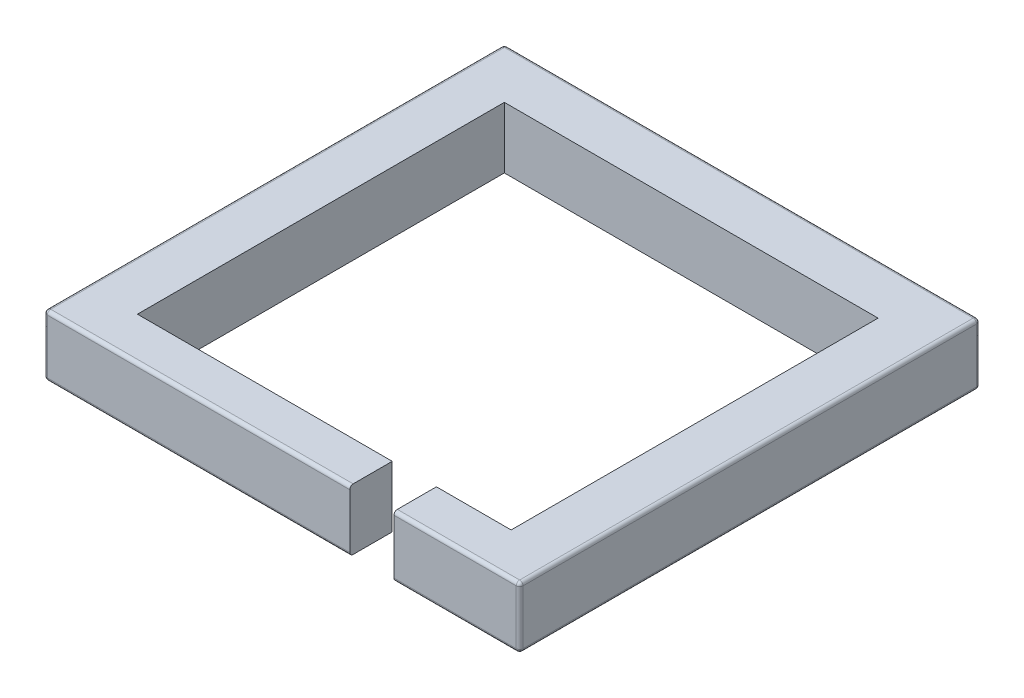
SolidWorks part; units mm, degrees
material "Polyurethane Foam Rigid"
ref_plane "Front Plane" through (0, 0, 0) normal (0, 0, 1) x (1, 0, 0)
ref_plane "Top Plane" through (0, 0, 0) normal (0, 1, 0) x (1, 0, 0)
ref_plane "Right Plane" through (0, 0, 0) normal (1, 0, 0) x (0, 0, -1)
sketch "Sketch2" plane through (0, 0, 0) normal (0, 1, 0) x (1, 0, 0)
  line L0 (-444.5, 438.15) -> (444.5, 438.15)
  line L1 (-349.25, -342.9) -> (349.25, -342.9)
  line L2 (-349.25, -342.9) -> (-349.25, 342.9)
  line L3 (-349.25, 342.9) -> (349.25, 342.9)
  line L4 (349.25, -342.9) -> (349.25, 342.9)
  line L5 (444.5, -422.275) -> (444.5, 438.15)
  line L6 (-349.25, 342.9) -> (349.25, -342.9) construction
  line L8 (-444.5, -422.275) -> (-444.5, 438.15)
  line L9 (-444.5, -438.15) -> (444.5, -438.15) construction
  line L10 (-444.5, -422.275) -> (444.5, -422.275)
  line L11 (444.5, -438.15) -> (444.5, 438.15) construction
  line L12 (-444.5, -438.15) -> (-444.5, 438.15) construction
  point P0 (0, 0)
  dimension "D1" = 685.8
  dimension "D2" = 698.5
  dimension "D4" = 79.375
  dimension "D3" = 95.25
extrude "Boss-Extrude1" add sketch "Sketch2" along normal blind 114.3
sketch "Sketch3" plane through (0, 114.3, 0) normal (0, 1, 0) x (1, 0, 0)
  line L0 (-349.25, -342.9) -> (349.25, -342.9) construction
  line L1 (127, -342.9) -> (209.55, -342.9)
  line L2 (127, -342.9) -> (127, -422.275)
  line L3 (127, -422.275) -> (209.55, -422.275)
  line L4 (209.55, -342.9) -> (209.55, -422.275)
  line L5 (-444.5, -422.275) -> (444.5, -422.275) construction
  line L6 (349.25, -342.9) -> (349.25, 342.9) construction
  dimension "D1" = 82.55
  dimension "D2" = 139.7
extrude "Cut-Extrude1" cut sketch "Sketch3" against normal through all
fillet "Fillet1" radius 6.35 14 edges at (-444.5, 0, -7.9375) (327.025, 0, 422.275) (-158.75, 0, 422.275) (444.5, 0, -7.9375) (0, 0, -438.15) (-444.5, 114.3, -7.9375) (327.025, 114.3, 422.275) (444.5, 114.3, -7.9375) (0, 114.3, -438.15) (-444.5, 57.15, -438.15) (444.5, 57.15, -438.15) (444.5, 57.15, 422.275) (-444.5, 57.15, 422.275) (-158.75, 114.3, 422.275)
